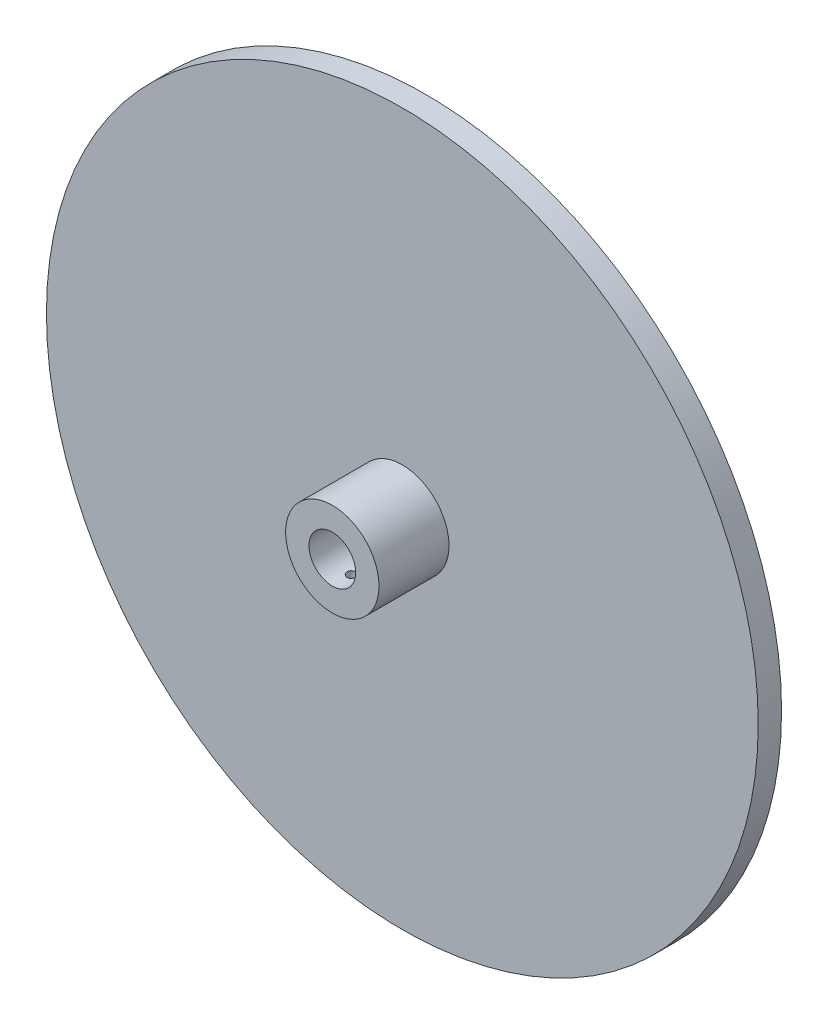
SolidWorks part; units mm, degrees
ref_plane "Front Plane" through (0, 0, 0) normal (0, 0, 1) x (1, 0, 0)
ref_plane "Top Plane" through (0, 0, 0) normal (0, 1, 0) x (1, 0, 0)
ref_plane "Right Plane" through (0, 0, 0) normal (1, 0, 0) x (0, 0, -1)
sketch "Sketch1" plane through (0, 0, 0) normal (0, 0, 1) x (1, 0, 0)
  circle A0 centre (0, 0) radius 152.5
  circle A1 centre (0, 0) radius 10
  dimension "D1" = 305
  dimension "D2" = 20
extrude "Boss-Extrude1" add sketch "Sketch1" along normal blind 10
sketch "Sketch2" plane through (0, 0, 10) normal (0, 0, 1) x (1, 0, 0)
  circle A0 centre (0, 0) radius 10
  circle A1 centre (0, 0) radius 20
  dimension "D1" = 40
extrude "Boss-Extrude2" add sketch "Sketch2" along normal blind 30
sketch "Sketch3" plane through (0, 0, 0) normal (0, 1, 0) x (1, 0, 0)
  circle A0 centre (0, -31.6386) radius 2
  dimension "D1" = 4
extrude "Cut-Extrude1" cut sketch "Sketch3" against normal blind 60
